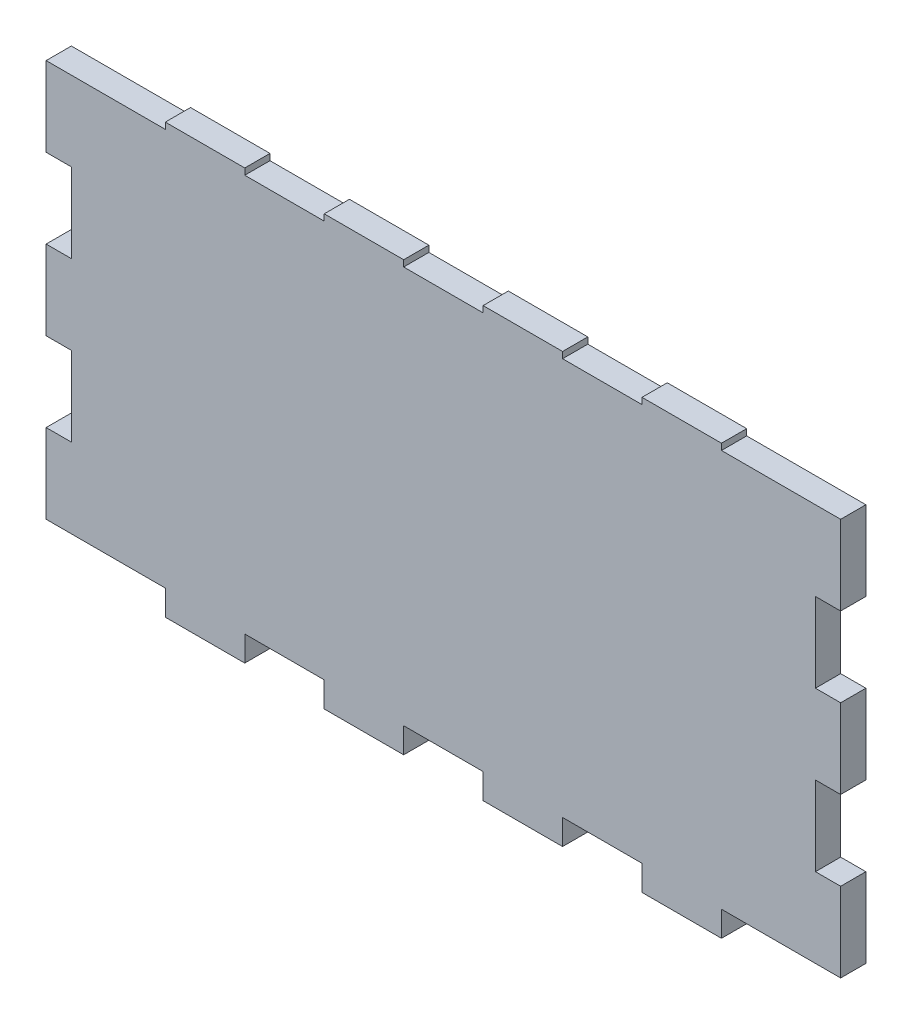
SolidWorks part; units mm, degrees
ref_plane "Front Plane" through (0, 0, 0) normal (0, 0, 1) x (1, 0, 0)
ref_plane "Top Plane" through (0, 0, 0) normal (0, 1, 0) x (1, 0, 0)
ref_plane "Right Plane" through (0, 0, 0) normal (1, 0, 0) x (0, 0, -1)
sketch "Sketch1" plane through (0, 0, 0) normal (0, 0, 1) x (1, 0, 0)
  line L0 (100, 100) -> (100, 0) construction
  line L1 (0, 0) -> (200, 0)
  line L2 (0, 0) -> (0, 100)
  line L3 (0, 100) -> (200, 100)
  line L4 (200, 0) -> (200, 100)
  line L5 (200, 50) -> (0, 50) construction
  line L6 (90, 0) -> (90, -6.35)
  line L7 (50, 0) -> (30, 0)
  line L8 (50, 0) -> (50, -6.35)
  line L9 (50, -6.35) -> (30, -6.35)
  line L10 (30, 0) -> (30, -6.35)
  line L11 (90, 0) -> (70, 0)
  line L12 (70, 0) -> (70, -6.35)
  line L13 (90, -6.35) -> (70, -6.35)
  line L14 (130, 0) -> (130, -6.35)
  line L15 (130, 0) -> (110, 0)
  line L16 (110, 0) -> (110, -6.35)
  line L17 (130, -6.35) -> (110, -6.35)
  line L18 (170, 0) -> (170, -6.35)
  line L19 (170, 0) -> (150, 0)
  line L20 (150, 0) -> (150, -6.35)
  line L21 (170, -6.35) -> (150, -6.35)
  line L22 (70, 100) -> (70, 101.5875)
  line L23 (30, 100) -> (50, 100)
  line L24 (30, 100) -> (30, 101.5875)
  line L25 (30, 101.5875) -> (50, 101.5875)
  line L26 (50, 100) -> (50, 101.5875)
  line L27 (70, 100) -> (90, 100)
  line L28 (90, 100) -> (90, 101.5875)
  line L29 (70, 101.5875) -> (90, 101.5875)
  line L30 (110, 100) -> (110, 101.5875)
  line L31 (110, 100) -> (130, 100)
  line L32 (130, 100) -> (130, 101.5875)
  line L33 (110, 101.5875) -> (130, 101.5875)
  line L34 (150, 100) -> (150, 101.5875)
  line L35 (150, 100) -> (170, 100)
  line L36 (170, 100) -> (170, 101.5875)
  line L37 (150, 101.5875) -> (170, 101.5875)
  line L38 (0, 40) -> (0, 20)
  line L39 (0, 80) -> (6.35, 80)
  line L40 (0, 80) -> (0, 60)
  line L41 (0, 60) -> (6.35, 60)
  line L42 (6.35, 80) -> (6.35, 60)
  line L43 (0, 40) -> (6.35, 40)
  line L44 (6.35, 40) -> (6.35, 20)
  line L45 (0, 20) -> (6.35, 20)
  line L46 (200, 40) -> (193.65, 40)
  line L47 (193.65, 40) -> (193.65, 20)
  line L48 (200, 20) -> (193.65, 20)
  line L49 (200, 40) -> (200, 20)
  line L50 (200, 60) -> (193.65, 60)
  line L51 (193.65, 80) -> (193.65, 60)
  line L52 (200, 80) -> (193.65, 80)
  line L53 (200, 80) -> (200, 60)
  point P46 (3.175, 60)
  dimension "D1" = 200
  dimension "D2" = 100
  dimension "D3" = 20
  dimension "D4" = 6.35
  dimension "D6" = 20
  dimension "D7" = 10
  dimension "D8" = 1.5875
  dimension "D9" = 20
  dimension "D11" = 20
  dimension "D12" = 10
  dimension "D13" = 20
  dimension "D15" = 10
  dimension "D16" = 6.35
  dimension "D17" = 20
  dimension "D5" = 4
  dimension "D10" = 4
  dimension "D14" = 2
extrude "Boss-Extrude1" add sketch "Sketch1" along normal blind 6.35 contours L52 L4 L3 L2 L39 L42 L41 L43 L44 L45 L1 L48 L47 L46 L50 L51 | L1 L10 L9 L8 | L13 L6 L1 L12 | L17 L14 L1 L16 | L21 L18 L1 L20 | L3 L26 L25 L24 | L29 L22 L3 L28 | L33 L30 L3 L32 | L37 L34 L3 L36
